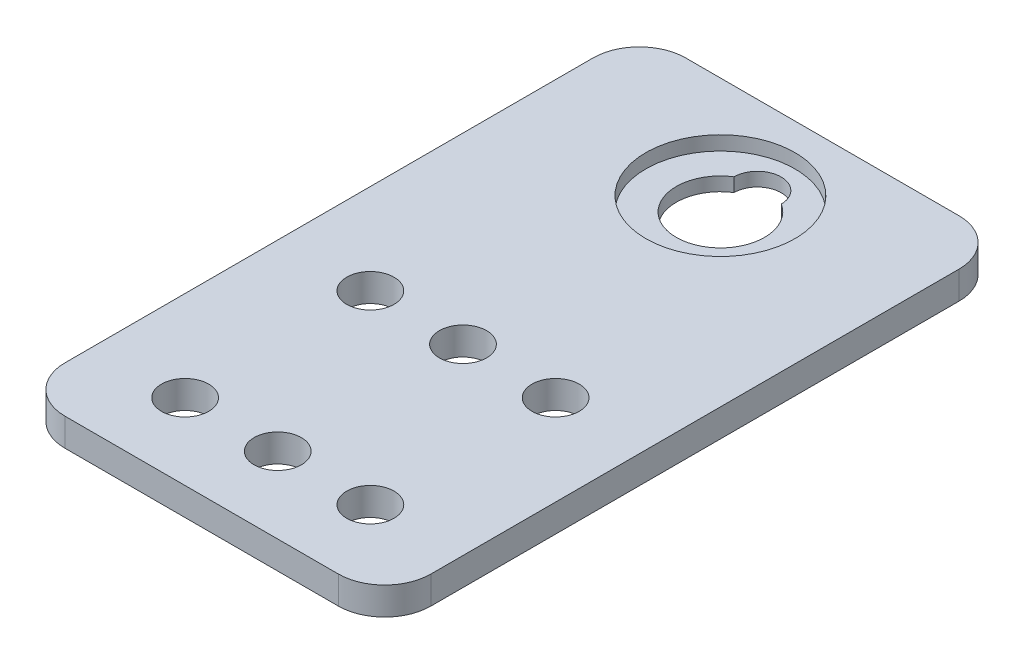
SolidWorks part; units mm, degrees
material "6061-T6 (SS)"
ref_plane "Front Plane" through (0, 0, 0) normal (0, 0, 1) x (1, 0, 0)
ref_plane "Top Plane" through (0, 0, 0) normal (0, 1, 0) x (1, 0, 0)
ref_plane "Right Plane" through (0, 0, 0) normal (1, 0, 0) x (0, 0, -1)
sketch "Sketch1" plane through (0, 0, 0) normal (0, 1, 0) x (1, 0, 0)
  line L0 (-19.75, 0) -> (0, 0) construction
  line L1 (14.75, -33.5) -> (-14.75, -33.5)
  line L2 (19.75, -28.5) -> (19.75, 28.5)
  line L3 (14.75, 33.5) -> (-14.75, 33.5)
  line L4 (-19.75, -28.5) -> (-19.75, 28.5)
  line L5 (0, 33.5) -> (0, 0) construction
  line L9 (10, -25.29) -> (0, -25.29) construction
  arc A0 (-14.75, -33.5) -> (-19.75, -28.5) centre (-14.75, -28.5) cw
  arc A1 (14.75, -33.5) -> (19.75, -28.5) centre (14.75, -28.5) ccw
  arc A2 (19.75, 28.5) -> (14.75, 33.5) centre (14.75, 28.5) ccw
  arc A3 (-14.75, 33.5) -> (-19.75, 28.5) centre (-14.75, 28.5) ccw
  circle A4 centre (0, 26.5) radius 2.55
  circle A7 centre (10, -25.29) radius 2.55
  circle A8 centre (10, -5.29) radius 2.55
  circle A9 centre (0, -25.29) radius 2.55
  circle A10 centre (0, -5.29) radius 2.55
  circle A11 centre (-10, -25.29) radius 2.55
  circle A12 centre (-10, -5.29) radius 2.55
  dimension "D2" = 5
  dimension "D3" = 7
  dimension "D7" = 20
  dimension "D10" = 3
  dimension "D8" = 9.75
  dimension "D6" = 5.1
  dimension "D1" = 67
  dimension "D9" = 39.5
  dimension "D11" = 10
  dimension "D12" = 8.21
extrude "Boss-Extrude1" add sketch "Sketch1" along normal blind 3
sketch "Sketch5" plane through (0, 3, 0) normal (0, 1, 0) x (1, 0, 0)
  circle A0 centre (0, 22.5) radius 8.002
  circle A1 centre (0, 26.5) radius 2.55 construction
  dimension "D2" = 4
  dimension "D3" = 16.004
  dimension "D1" = 0
hole_wizard "CBORE for #00 Binding Head Machine Screw1" positions "Sketch7" profile "Sketch6" counterbore size "#00" standard "ANSI Inch" end condition through all
sketch "Sketch7" plane through (0, 3, 0) normal (0, 1, 0) x (1, 0, 0)
  point P0 (0, 22.5)
sketch "Sketch6" plane through (0, 3, -22.5) normal (1, 0, 0) x (0, 0, 1)
  line L0 (0, 0) -> (0, 3)
  line L1 (0, 3) -> (4.7625, 3)
  line L3 (4.7625, 3) -> (4.7625, 1.524)
  line L4 (4.7625, 1.524) -> (8.0518, 1.524)
  line L5 (8.0518, 1.524) -> (8.0518, 0)
  line L7 (8.0518, 0) -> (0, 0)
  line L11 (0, -6.35) -> (0, 107.95) construction
  dimension "Thru Hole Dia." = 9.525
  dimension "Thru Hole Depth" = 3
  dimension "C'Bore Dia." = 16.1036
  dimension "C'Bore Depth" = 1.524
